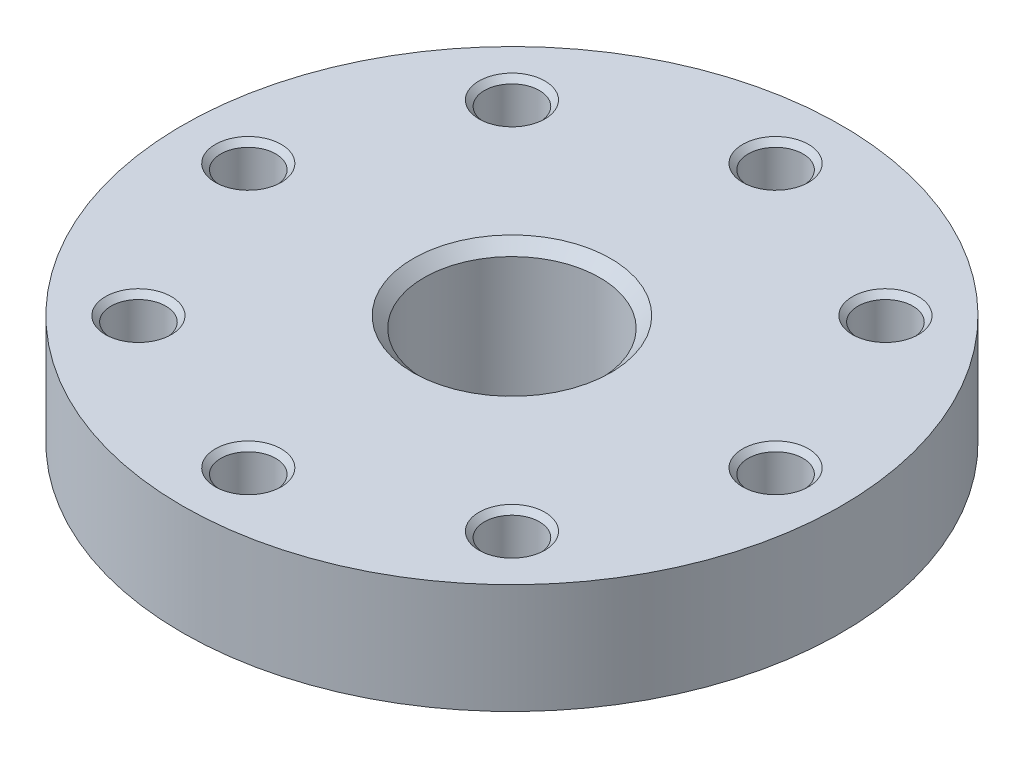
SolidWorks part; units mm, degrees
ref_plane "Front Plane" through (0, 0, 0) normal (0, 0, 1) x (1, 0, 0)
ref_plane "Top Plane" through (0, 0, 0) normal (0, 1, 0) x (1, 0, 0)
ref_plane "Right Plane" through (0, 0, 0) normal (1, 0, 0) x (0, 0, -1)
sketch "Sketch1" plane through (0, 0, 0) normal (0, 1, 0) x (1, 0, 0)
  circle A0 centre (0, 0) radius 15
extrude "Boss-Extrude1" add sketch "Sketch1" along normal blind 5
sketch "Sketch2" plane through (0, 5, 0) normal (0, 1, 0) x (1, 0, 0)
  line L0 (-12, 0) -> (12, 0) construction
  line L1 (0, -12) -> (0, 12) construction
  line L2 (-8.5, 8.5) -> (8.5, 8.5) construction
  line L3 (-8.5, 8.5) -> (-8.5, -8.5) construction
  line L4 (-8.5, -8.5) -> (8.5, -8.5) construction
  line L5 (8.5, -8.5) -> (8.5, 8.5) construction
  circle A0 centre (0, 12) radius 1.25
  circle A1 centre (-12, 0) radius 1.25
  circle A2 centre (0, -12) radius 1.25
  circle A3 centre (12, 0) radius 1.25
  circle A4 centre (-8.5, 8.5) radius 1.25
  circle A5 centre (-8.5, -8.5) radius 1.25
  circle A6 centre (8.5, 8.5) radius 1.25
  circle A7 centre (8.5, -8.5) radius 1.25
  point P5 (0, 0)
  point P9 (0, 0)
  point P16 (0, 8.5)
  point P19 (-8.5, 0)
extrude "Cut-Extrude1" cut sketch "Sketch2" against normal through all
sketch "Sketch3" plane through (0, 0, 0) normal (0, 1, 0) x (1, 0, 0)
  circle A0 centre (0, 0) radius 6
extrude "Boss-Extrude2" add sketch "Sketch3" against normal blind 1.5
sketch "Sketch4" plane through (0, -1.5, 0) normal (0, -1, 0) x (1, 0, 0)
  circle A0 centre (0, 0) radius 1.5
extrude "Cut-Extrude2" cut sketch "Sketch4" against normal blind 1.5
chamfer "Chamfer5" distance 0.25 angle 45 16 edges at (-12, 0, 1.25) (-8.5, 0, -7.25) (0, 0, -10.75) (8.5, 0, -7.25) (12, 0, 1.25) (8.5, 0, 9.75) (0, 0, 13.25) (-8.5, 0, 9.75) (8.5, 5, -7.25) (0, 5, -10.75) (-8.5, 5, -7.25) (-12, 5, 1.25) (-8.5, 5, 9.75) (0, 5, 13.25) (8.5, 5, 9.75) (12, 5, 1.25)
sketch "Sketch5" plane through (0, 5, 0) normal (0, 1, 0) x (1, 0, 0)
  circle A1 centre (0, 0) radius 4
extrude "Cut-Extrude3" cut sketch "Sketch5" against normal blind 6
chamfer "Chamfer7" distance 0.5 angle 45 1 edges at (0, 5, 4)
